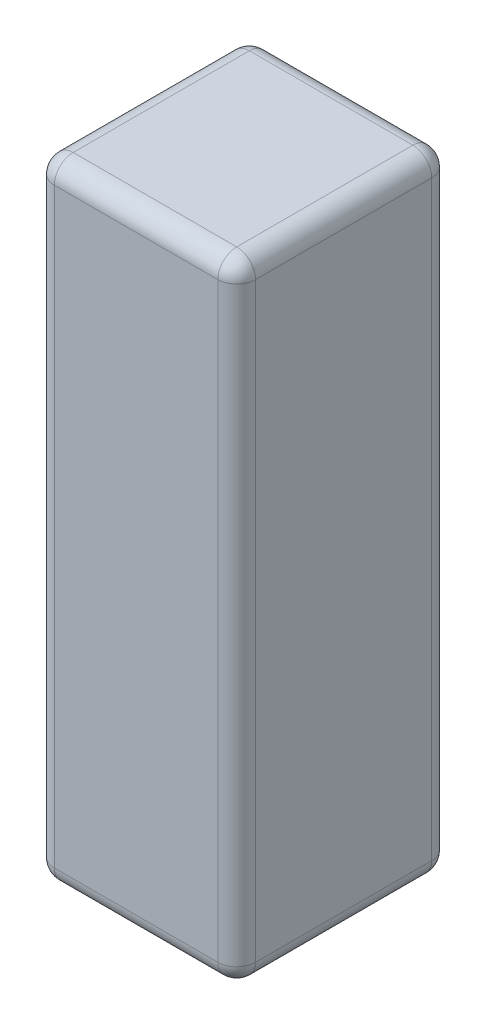
SolidWorks part; units mm, degrees
ref_plane "Front Plane" through (0, 0, 0) normal (0, 0, 1) x (1, 0, 0)
ref_plane "Top Plane" through (0, 0, 0) normal (0, 1, 0) x (1, 0, 0)
ref_plane "Right Plane" through (0, 0, 0) normal (1, 0, 0) x (0, 0, -1)
sketch "Sketch1" plane through (0, 0, 0) normal (0, 0, 1) x (1, 0, 0)
  line L1 (30.306, 2.6506) -> (62.306, 2.6506)
  line L2 (30.306, 2.6506) -> (30.306, -97.3494)
  line L3 (30.306, -97.3494) -> (62.306, -97.3494)
  line L4 (62.306, 2.6506) -> (62.306, -97.3494)
extrude "Boss-Extrude1" add sketch "Sketch1" along normal blind 34
fillet "Fillet1" radius 3 12 edges at (62.306, -47.3494, 0) (30.306, -47.3494, 0) (62.306, -47.3494, 34) (30.306, -47.3494, 34) (62.306, 2.6506, 17) (46.306, 2.6506, 34) (30.306, 2.6506, 17) (46.306, 2.6506, 0) (30.306, -97.3494, 17) (46.306, -97.3494, 34) (62.306, -97.3494, 17) (46.306, -97.3494, 0)
